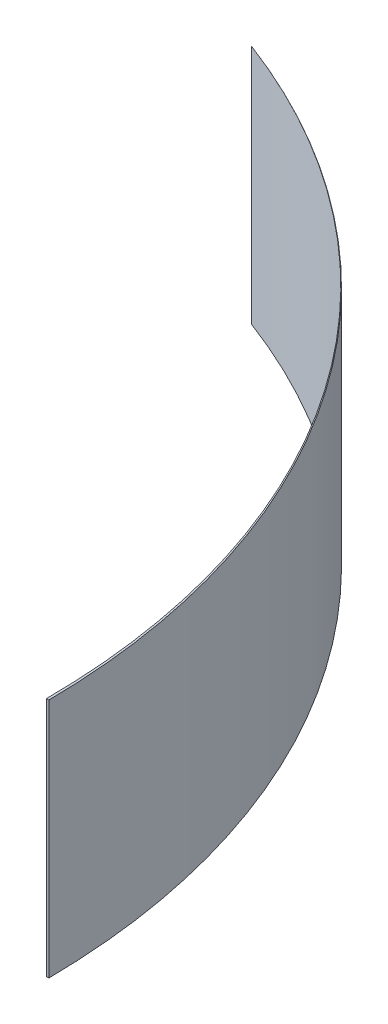
SolidWorks part; units mm, degrees
material "Acrílico (médio-alto impacto)"
ref_plane "Plano frontal" through (0, 0, 0) normal (0, 0, 1) x (1, 0, 0)
ref_plane "Plano superior" through (0, 0, 0) normal (0, 1, 0) x (1, 0, 0)
ref_plane "Plano direito" through (0, 0, 0) normal (1, 0, 0) x (0, 0, -1)
sketch "Esboço2" plane through (0, 0, 0) normal (0, 1, 0) x (1, 0, 0)
  line L0 (0, 0) -> (4, 0)
  line L6 (-1190.9575, 1186.0361) -> (-1190.9575, 1186.0561)
  arc A0 (-1190.9575, 1186.0361) -> (0, 0) centre (-1189.9934, -3.9635) cw
  arc A2 (-1190.9575, 1186.0561) -> (4, 0) centre (-1190.9575, -8.9348) cw
  dimension "D1" = 1190
extrude "Ressalto-extrusão1" add sketch "Esboço2" along normal blind 400
